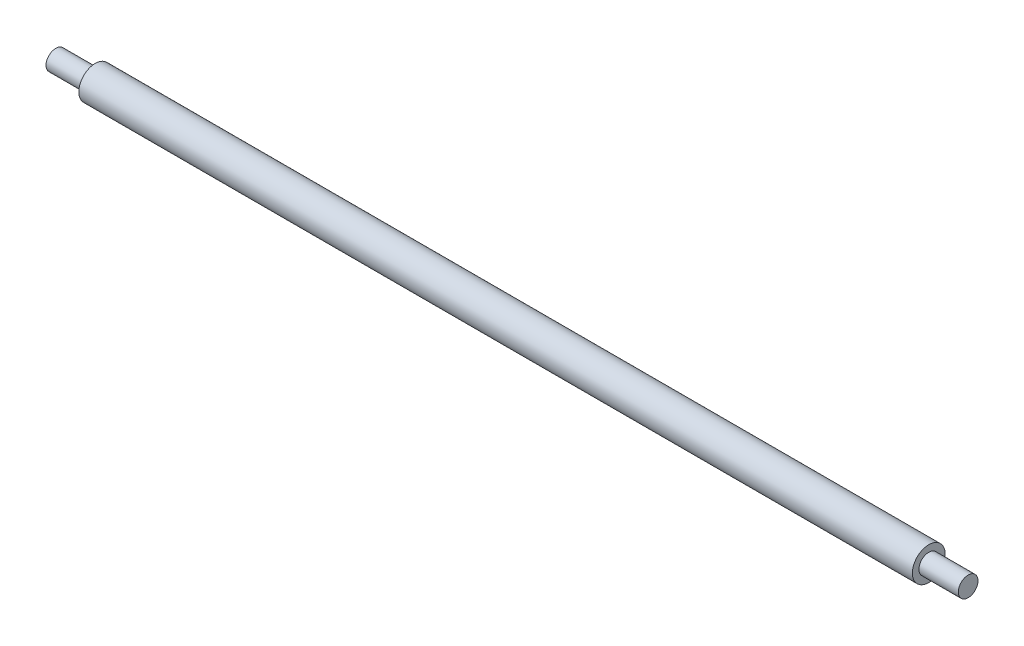
SolidWorks part; units mm, degrees
material "Stainless Steel (ferritic)"
ref_plane "Front Plane" through (0, 0, 0) normal (0, 0, 1) x (1, 0, 0)
ref_plane "Top Plane" through (0, 0, 0) normal (0, 1, 0) x (1, 0, 0)
ref_plane "Right Plane" through (0, 0, 0) normal (1, 0, 0) x (0, 0, -1)
sketch "Sketch1" plane through (0, 0, 0) normal (1, 0, 0) x (0, 0, -1)
  circle A0 centre (0, 0) radius 2.5
  dimension "D1" = 5
extrude "Boss-Extrude1" add sketch "Sketch1" along normal mid plane 127
sketch "Sketch2" plane through (63.5, 0, 0) normal (1, 0, 0) x (0, 0, -1)
  circle A0 centre (0, 0) radius 1.5
  dimension "D1" = 3
extrude "Boss-Extrude2" add sketch "Sketch2" along normal blind 6
sketch "Sketch3" plane through (-63.5, 0, 0) normal (-1, 0, 0) x (0, 0, 1)
  circle A0 centre (0, 0) radius 1.5
  dimension "D1" = 3
extrude "Boss-Extrude3" add sketch "Sketch3" along normal blind 6
equation "\"e\"=4.82414"
